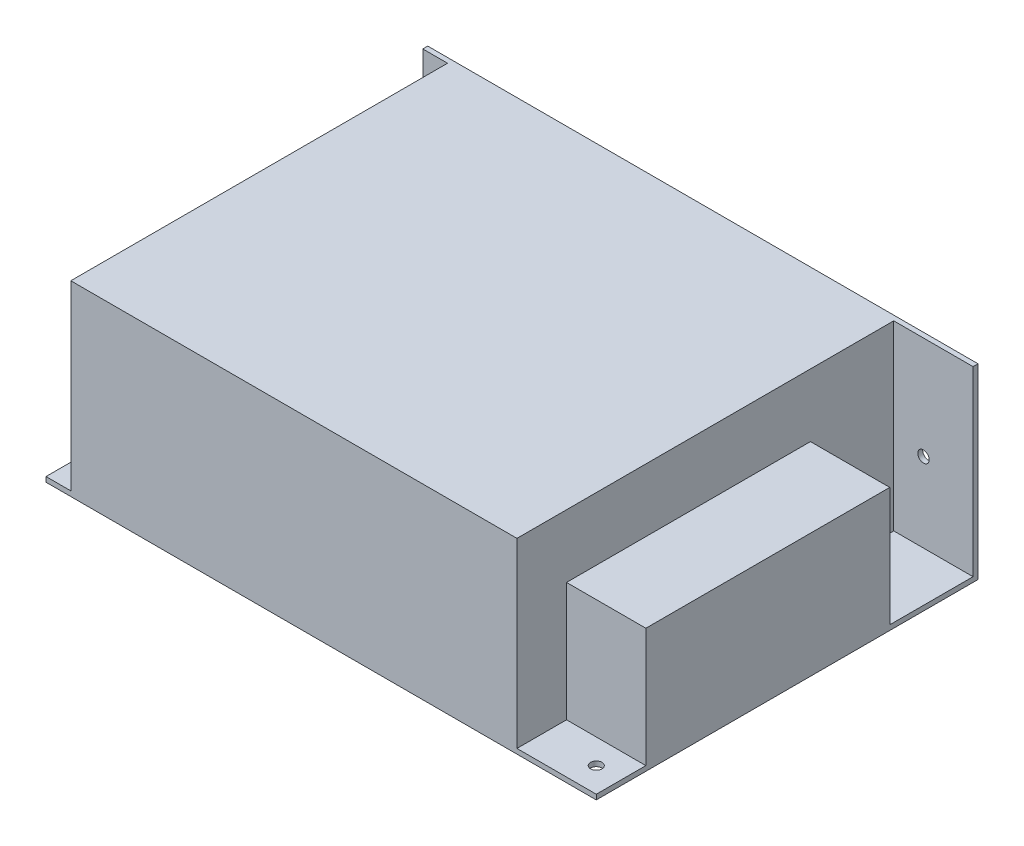
SolidWorks part; units mm, degrees
ref_plane "Plano frontal" through (0, 0, 0) normal (0, 0, 1) x (1, 0, 0)
ref_plane "Plano superior" through (0, 0, 0) normal (0, 1, 0) x (1, 0, 0)
ref_plane "Plano direito" through (0, 0, 0) normal (1, 0, 0) x (0, 0, -1)
sketch "Esboço1" plane through (0, 0, 0) normal (0, 1, 0) x (1, 0, 0)
  line L1 (55.5, -38.5) -> (-55.5, -38.5)
  line L2 (55.5, -38.5) -> (55.5, 38.5)
  line L3 (55.5, 38.5) -> (-55.5, 38.5)
  line L4 (-55.5, -38.5) -> (-55.5, 38.5)
  line L5 (55.5, -38.5) -> (-55.5, 38.5) construction
  line L6 (55.5, 38.5) -> (-55.5, -38.5) construction
  point P0 (0, 0)
  dimension "D1" = 111
  dimension "D2" = 77
extrude "Ressalto-extrusão1" add sketch "Esboço1" along normal blind 1
sketch "Esboço2" plane through (0, 1, 0) normal (0, 1, 0) x (1, 0, 0)
  line L0 (0, -44.2237) -> (0, 43.8634) construction
  line L1 (55.5, -38.5) -> (55.5, 38.5) construction
  line L2 (-55.5, 38.5) -> (55.5, 38.5)
  line L3 (-55.5, 38.5) -> (-55.5, 37.5)
  line L4 (-55.5, 37.5) -> (55.5, 37.5)
  line L5 (55.5, 38.5) -> (55.5, 37.5)
  dimension "D1" = 1
extrude "Ressalto-extrusão2" add sketch "Esboço2" along normal blind 36.7
sketch "Esboço3" plane through (0, 1, 0) normal (0, 1, 0) x (1, 0, 0)
  line L0 (-55.5, 37.5) -> (55.5, 37.5) construction
  line L1 (-50.5, 37.5) -> (39.5, 37.5)
  line L2 (-50.5, 37.5) -> (-50.5, -38.5)
  line L3 (-50.5, -38.5) -> (39.5, -38.5)
  line L4 (39.5, 37.5) -> (39.5, -38.5)
  line L5 (-55.5, -38.5) -> (55.5, -38.5) construction
  line L6 (-55.5, 37.5) -> (-55.5, -38.5) construction
  line L7 (55.5, -38.5) -> (55.5, 37.5) construction
  dimension "D1" = 5
  dimension "D2" = 16
extrude "Ressalto-extrusão3" add sketch "Esboço3" along normal blind 36.7
sketch "Esboço4" plane through (0, 1, 0) normal (0, 1, 0) x (1, 0, 0)
  line L0 (55.5, -38.5) -> (55.5, 37.5) construction
  line L1 (55.5, 20.7) -> (39.5, 20.7)
  line L2 (55.5, 20.7) -> (55.5, -28.5)
  line L3 (55.5, -28.5) -> (39.5, -28.5)
  line L4 (39.5, 20.7) -> (39.5, -28.5)
  line L5 (39.5, -38.5) -> (39.5, 37.5) construction
  line L6 (39.5, -38.5) -> (55.5, -38.5) construction
  dimension "D1" = 49.2
  dimension "D2" = 10
extrude "Ressalto-extrusão4" add sketch "Esboço4" along normal blind 24
sketch "Esboço5" plane through (0, 0, -38.5) normal (0, 0, -1) x (-1, 0, 0)
  line L0 (0, -13.1243) -> (0, 51.5449) construction
  line L1 (-55.5, 37.7) -> (-55.5, 0) construction
  line L2 (-55.5, 0) -> (55.5, 0) construction
  line L3 (55.5, 37.7) -> (55.5, 0) construction
  line L4 (57.4444, 29.0065) -> (49.4298, 29.0065) construction
  line L5 (55.5, 30.6065) -> (52.6, 30.6065)
  line L6 (55.5, 30.6065) -> (55.5, 27.4065)
  line L7 (55.5, 27.4065) -> (52.6, 27.4065)
  circle A0 centre (-45.5, 17) radius 1.15
  circle A1 centre (43.5, 13) radius 1.15
  arc A3 (52.6, 30.6065) -> (52.6, 27.4065) centre (52.6, 29.0065) ccw
  dimension "D1" = 2.3
  dimension "D2" = 10
  dimension "D3" = 17
  dimension "D4" = 12
  dimension "D5" = 2.3
  dimension "D6" = 13
  dimension "D7" = 3.2
  dimension "D9" = 2.9
extrude "Corte-extrusão1" cut sketch "Esboço5" against normal blind 5
sketch "Esboço6" plane through (0, 0, 0) normal (0, -1, 0) x (1, 0, 0)
  line L0 (-55.5, 38.5) -> (55.5, 38.5) construction
  line L1 (-55.5, -38.5) -> (-55.5, 38.5) construction
  line L2 (55.5, 38.5) -> (55.5, -38.5) construction
  line L3 (55.5, -38.5) -> (-55.5, -38.5) construction
  circle A0 centre (-42.5, 31.5) radius 1.15
  circle A1 centre (50.5, 33.5) radius 1.15
  circle A2 centre (-13, 13) radius 1.15
  circle A3 centre (23.5, 13.5) radius 1.15
  circle A4 centre (-13, -15) radius 1.15
  dimension "D1" = 2.3
  dimension "D2" = 7
  dimension "D3" = 13
  dimension "D4" = 2.3
  dimension "D5" = 5
  dimension "D6" = 5
  dimension "D7" = 42.5
  dimension "D8" = 25.5
  dimension "D9" = 42.5
  dimension "D10" = 23.5
  dimension "D11" = 25
  dimension "D12" = 32
extrude "Corte-extrusão2" cut sketch "Esboço6" against normal blind 5
